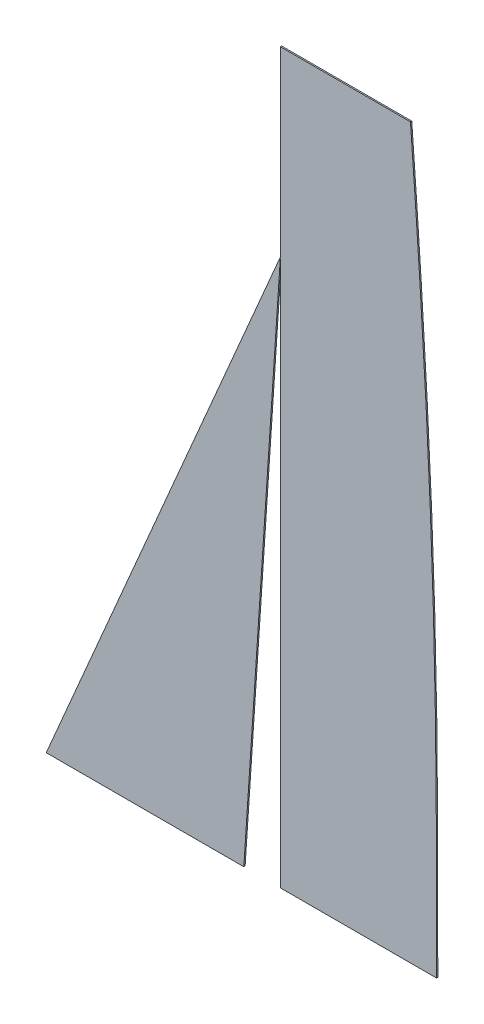
SolidWorks part; units mm, degrees
material "ABS PC"
ref_plane "Front Plane" through (0, 0, 0) normal (0, 0, 1) x (1, 0, 0)
ref_plane "Top Plane" through (0, 0, 0) normal (0, 1, 0) x (1, 0, 0)
ref_plane "Right Plane" through (0, 0, 0) normal (1, 0, 0) x (0, 0, -1)
sketch "Sketch1" plane through (0, 0, 0) normal (0, 0, 1) x (1, 0, 0)
  line L0 (0, 0) -> (0, 1422.4)
  line L1 (0, 1422.4) -> (254, 1422.4)
  line L2 (304.8, 0) -> (0, 0)
  line L3 (304.8, -639.4863) -> (304.8, 639.4863) construction
  spline S0 degree 3 poles (254, 1422.4) (307.2868, 718.6861) (304.8, 400.6934) (304.8, 0) knots 0 0 0 0 1 1 1 1
  dimension "D1" = 1422.4
  dimension "D2" = 304.8
  dimension "D3" = 254
extrude "Boss-Extrude1" add sketch "Sketch1" along normal blind 2.54
sketch "Sketch2" plane through (0, 0, 0) normal (0, 0, 1) x (1, 0, 0)
  line L0 (0, 0) -> (0, 1066.8)
  line L1 (0, 1422.4) -> (0, 0) construction
  line L2 (0, 1066.8) -> (-457.2, 0)
  line L3 (-457.2, 0) -> (0, 0)
  line L4 (0, 1066.8) -> (-71.3735, 0)
  dimension "D1" = 1066.8
  dimension "D2" = 457.2
extrude "Boss-Extrude3" add sketch "Sketch2" along normal blind 2.54 separate body contours L4 L2 L3
